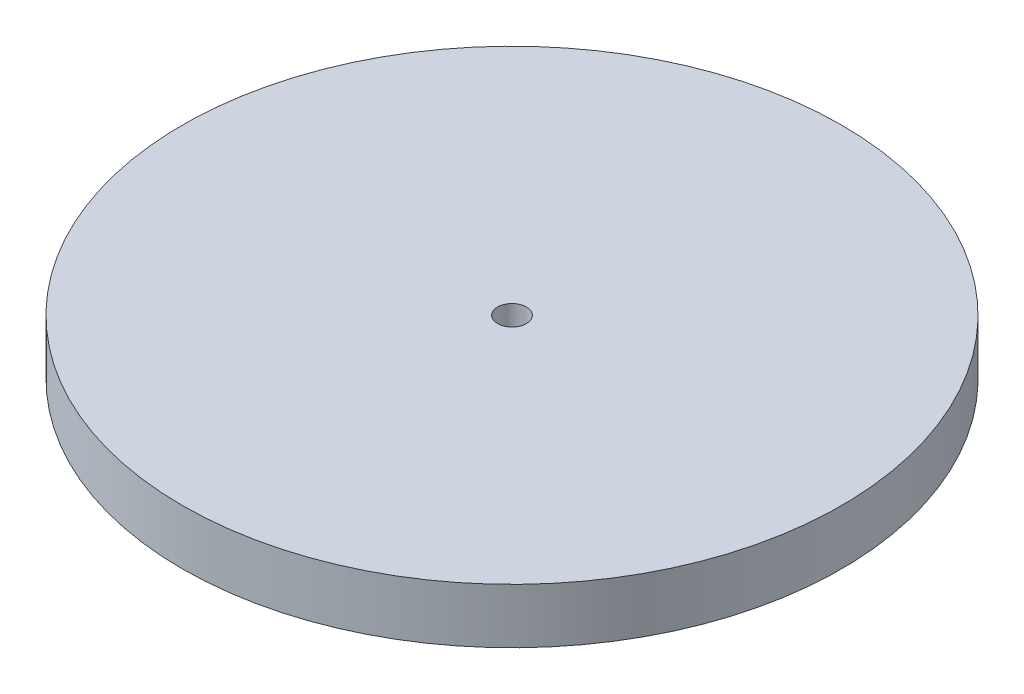
SolidWorks part; units mm, degrees
ref_plane "Front Plane" through (0, 0, 0) normal (0, 0, 1) x (1, 0, 0)
ref_plane "Top Plane" through (0, 0, 0) normal (0, 1, 0) x (1, 0, 0)
ref_plane "Right Plane" through (0, 0, 0) normal (1, 0, 0) x (0, 0, -1)
sketch "Sketch1" plane through (0, 0, 0) normal (0, 1, 0) x (1, 0, 0)
  circle A0 centre (0, 0) radius 45.72
  circle A1 centre (0, 0) radius 2
extrude "Boss-Extrude1" add sketch "Sketch1" along normal blind 7.62
equation "\"D1@Boss-Extrude1\"=\"MDF\""
equation "\"MDF\" = 0.3in"
